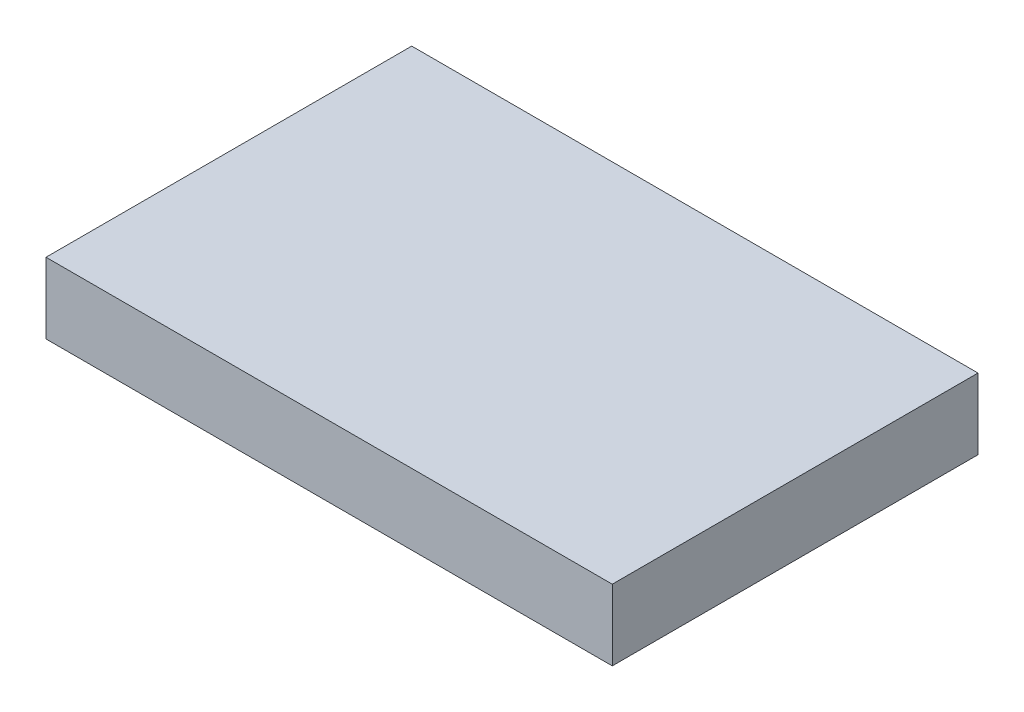
SolidWorks part; units mm, degrees
ref_plane "Front Plane" through (0, 0, 0) normal (0, 0, 1) x (1, 0, 0)
ref_plane "Top Plane" through (0, 0, 0) normal (0, 1, 0) x (1, 0, 0)
ref_plane "Right Plane" through (0, 0, 0) normal (1, 0, 0) x (0, 0, -1)
sketch "Sketch1" plane through (0, 0, 0) normal (0, 1, 0) x (1, 0, 0)
  line L1 (-30.48, -19.685) -> (30.48, -19.685)
  line L2 (-30.48, -19.685) -> (-30.48, 19.685)
  line L3 (-30.48, 19.685) -> (30.48, 19.685)
  line L4 (30.48, -19.685) -> (30.48, 19.685)
  line L5 (-30.48, -19.685) -> (30.48, 19.685) construction
  line L6 (-30.48, 19.685) -> (30.48, -19.685) construction
  point P0 (0, 0)
  dimension "D1" = 60.96
  dimension "D2" = 39.37
extrude "Boss-Extrude1" add sketch "Sketch1" along normal blind 7.62
